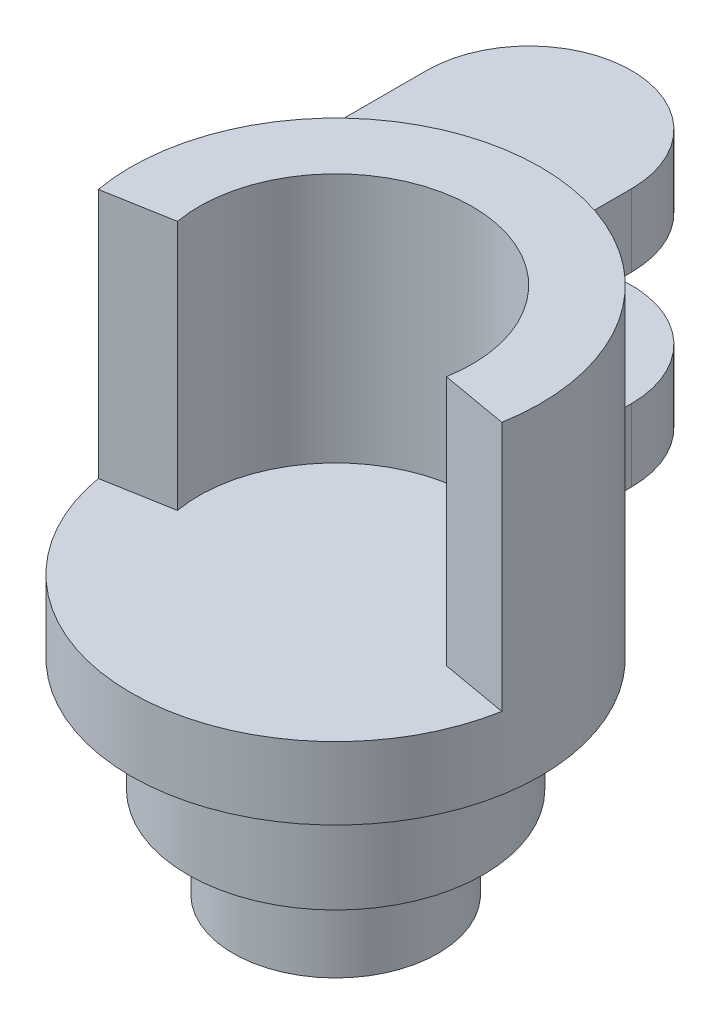
SolidWorks part; units mm, degrees
ref_plane "Front Plane" through (0, 0, 0) normal (0, 0, 1) x (1, 0, 0)
ref_plane "Top Plane" through (0, 0, 0) normal (0, 1, 0) x (1, 0, 0)
ref_plane "Right Plane" through (0, 0, 0) normal (1, 0, 0) x (0, 0, -1)
sketch "Sketch1" plane through (0, 0, 0) normal (0, 1, 0) x (1, 0, 0)
  circle A0 centre (0, 0) radius 9
  dimension "D1" = 18
extrude "Boss-Extrude1" add sketch "Sketch1" along normal blind 3.175
sketch "Sketch3" plane through (0, 3.175, 0) normal (0, 1, 0) x (1, 0, 0)
  line L1 (-8.8633, -1.5628) -> (-5.9088, -1.0419)
  line L2 (5.9088, -1.0419) -> (8.8633, -1.5628)
  line L3 (-8.8633, -1.5628) -> (8.8633, -1.5628) construction
  arc A0 (8.8633, -1.5628) -> (-8.8633, -1.5628) centre (0, 0) ccw
  circle A1 centre (0, 0) radius 9 construction
  arc A2 (5.9088, -1.0419) -> (-5.9088, -1.0419) centre (0, 0) ccw
  dimension "D1" = 160
  dimension "D2" = 3
extrude "Boss-Extrude2" add sketch "Sketch3" along normal blind 11 contours L2 A0 L1 A2
sketch "Sketch4" plane through (0, 0, 0) normal (0, -1, 0) x (1, 0, 0)
  circle A0 centre (0, 0) radius 6.5
  circle A1 centre (0, 0) radius 9 construction
  dimension "D1" = 13
extrude "Boss-Extrude3" add sketch "Sketch4" along normal blind 5 contours A0
sketch "Sketch5" plane through (0, -5, 0) normal (0, -1, 0) x (1, 0, 0)
  circle A0 centre (0, 0) radius 4.5
  circle A1 centre (0, 0) radius 6.5 construction
  dimension "D1" = 9
extrude "Boss-Extrude4" add sketch "Sketch5" along normal blind 4 contours A0
sketch "Sketch6" plane through (0, 0, 0) normal (0, 1, 0) x (1, 0, 0)
  line L0 (-9, 0) -> (-9, 13)
  line L1 (0, 9) -> (0, 13)
  arc A0 (-9, 13) -> (0, 13) centre (-4.5, 13) cw
  arc A1 (8.8633, -1.5628) -> (-8.8633, -1.5628) centre (0, 0) ccw construction
  arc A2 (0, 9) -> (-9, 0) centre (0, 0) ccw
  dimension "D1" = 4
extrude "Boss-Extrude5" add sketch "Sketch6" along normal up to surface (3.175 mm away) contours L0 A0 L1 A2 up to face at (0, 3.175, 1.4012)
ref_plane "Plane1" through (0, 8.175, 0) normal (0, 1, 0) x (1, 0, 0)
sketch "Sketch7" plane through (0, 8.175, 0) normal (0, 1, 0) x (1, 0, 0)
  line L2 (0, 9) -> (0, 13)
  line L3 (-9, 13) -> (-9, 0)
  line L4 (0, 9) -> (0, 13)
  line L5 (-9, 13) -> (-9, 0)
  arc A2 (0, 9) -> (-9, 0) centre (0, 0) ccw
  arc A3 (0, 13) -> (-9, 13) centre (-4.5, 13) ccw
  arc A4 (0, 9) -> (-9, 0) centre (0, 0) ccw
  arc A5 (0, 13) -> (-9, 13) centre (-4.5, 13) ccw
  dimension "D1" = 0
extrude "Boss-Extrude6" add sketch "Sketch7" along normal blind 3.175
